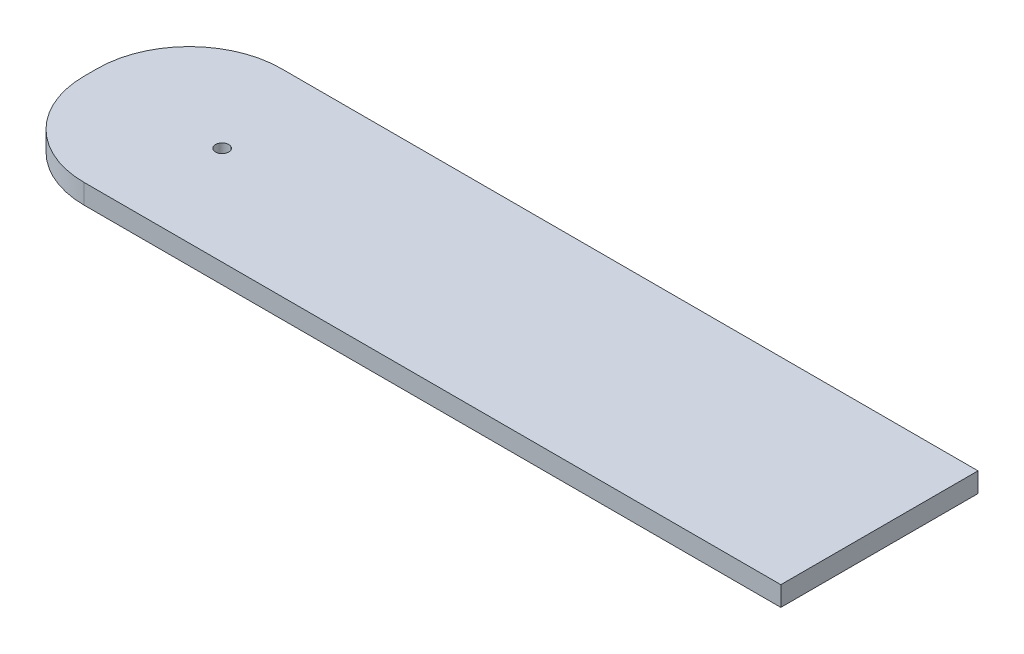
SolidWorks part; units mm, degrees
ref_plane "Front Plane" through (0, 0, 0) normal (0, 0, 1) x (1, 0, 0)
ref_plane "Top Plane" through (0, 0, 0) normal (0, 1, 0) x (1, 0, 0)
ref_plane "Right Plane" through (0, 0, 0) normal (1, 0, 0) x (0, 0, -1)
sketch "Sketch1" plane through (0, 0, 0) normal (0, 1, 0) x (1, 0, 0)
  line L1 (0, 0) -> (120, 0)
  line L2 (0, 0) -> (0, 30)
  line L3 (0, 30) -> (120, 30)
  line L4 (120, 0) -> (120, 30)
  dimension "D1" = 30
  dimension "D2" = 120
extrude "Boss-Extrude1" add sketch "Sketch1" along normal blind 3
sketch "Sketch2" plane through (0, 3, 0) normal (0, 1, 0) x (1, 0, 0)
sketch "Sketch3" plane through (0, 3, 0) normal (0, 1, 0) x (1, 0, 0)
  line L0 (0, 30) -> (0, 0) construction
  line L1 (0, 0) -> (120, 0) construction
  circle A0 centre (20, 15) radius 1
  dimension "D1" = 2
  dimension "D2" = 20
  dimension "D3" = 15
extrude "Cut-Extrude1" cut sketch "Sketch3" against normal through all
fillet "Fillet1" radius 14 2 edges at (0, 1.5, -30) (0, 1.5, 0)
